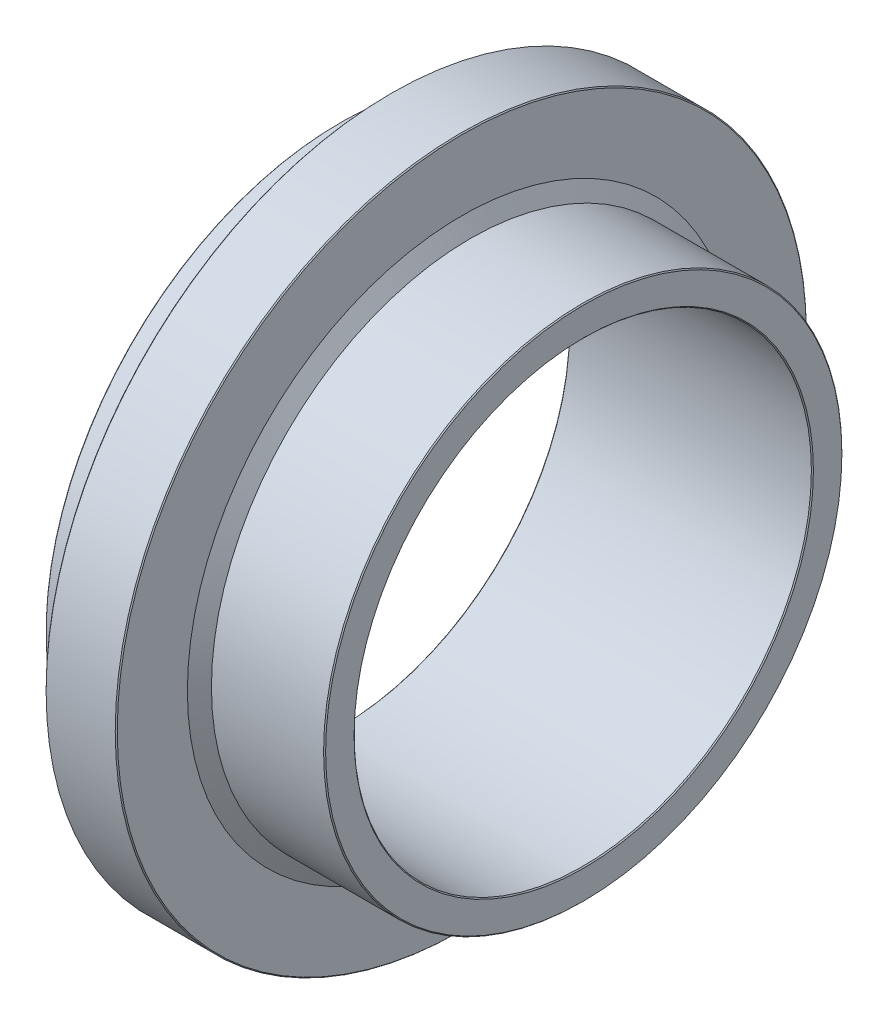
SolidWorks part; units mm, degrees
ref_plane "Plan de face" through (0, 0, 0) normal (0, 0, 1) x (1, 0, 0)
ref_plane "Plan de dessus" through (0, 0, 0) normal (0, 1, 0) x (1, 0, 0)
ref_plane "Plan de droite" through (0, 0, 0) normal (1, 0, 0) x (0, 0, -1)
sketch "Esquisse1" plane through (0, 0, 0) normal (0, 0, 1) x (1, 0, 0)
  line L0 (0, 0) -> (-131.0238, 0) construction
  line L1 (0, 45.2) -> (0, 50.8)
  line L2 (-0.2, 51) -> (-22.2679, 51)
  line L3 (-22.2679, 51) -> (-24, 54)
  line L4 (-24, 54) -> (-24, 67.8)
  line L5 (-24.2, 68) -> (-37.8, 68)
  line L6 (-38, 67.8) -> (-38, 58)
  line L7 (-38, 58) -> (-47.8, 58)
  line L8 (-48, 57.8) -> (-48, 45.2)
  line L9 (-47.8, 45) -> (-0.2, 45)
  line L10 (-47.8, 58) -> (-48, 57.8)
  line L11 (-37.8, 68) -> (-38, 67.8)
  line L12 (-24, 67.8) -> (-24.2, 68)
  line L13 (0, 50.8) -> (-0.2, 51)
  line L14 (-0.2, 45) -> (0, 45.2)
  line L15 (-48, 45.2) -> (-47.8, 45)
  point P3 (0, 45)
  point P4 (0, 51)
  point P5 (-53.7007, 51)
  point P7 (-24, 51)
  point P8 (-24, 68)
  point P9 (-38, 68)
  point P11 (-48, 58)
  point P12 (-48, 45)
  point P13 (-53.7007, 51)
  point P14 (-52.2632, 51)
  dimension "D1" = 116
  dimension "D2" = 90
  dimension "D3" = 136
  dimension "D4" = 102
  dimension "D5" = 48
  dimension "D6" = 24
  dimension "D7" = 10
  dimension "D8" = 3
  dimension "D9" = 30
  dimension "D10" = 0.2
  dimension "D11" = 45
  dimension "D12" = 0.2
  dimension "D13" = 45
  dimension "D14" = 0.2
  dimension "D15" = 45
  dimension "D16" = 0.2
  dimension "D17" = 45
  dimension "D18" = 0.2
  dimension "D19" = 45
  dimension "D20" = 0.2
  dimension "D21" = 45
revolve "Révolution1" add sketch "Esquisse1" angle 360 about L0
